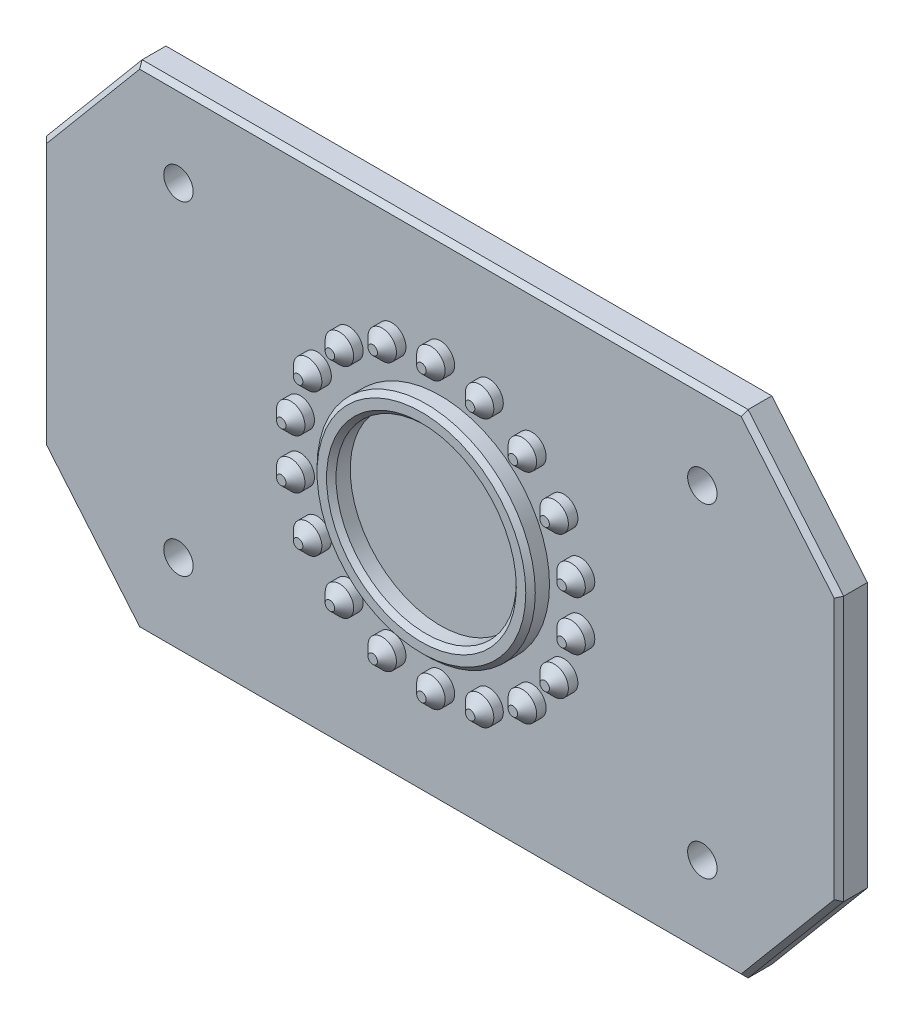
SolidWorks part; units mm, degrees
ref_plane "Front Plane" through (0, 0, 0) normal (0, 0, 1) x (1, 0, 0)
ref_plane "Top Plane" through (0, 0, 0) normal (0, 1, 0) x (1, 0, 0)
ref_plane "Right Plane" through (0, 0, 0) normal (1, 0, 0) x (0, 0, -1)
sketch "Sketch1" plane through (0, 0, 0) normal (0, 0, 1) x (1, 0, 0)
  line L0 (-110, 14.6505) -> (-99.9308, 2.6505) construction
  line L6 (-99.9308, 54.5343) -> (-110, 42.5343) construction
  line L7 (-110, 42.5343) -> (-110, 14.6505) construction
  line L8 (-26, 14.6505) -> (-26, 42.5343) construction
  line L9 (-26, 42.5343) -> (-36.0692, 54.5343) construction
  line L15 (-36.0692, 2.6505) -> (-26, 14.6505) construction
  line L16 (-110, 14.6505) -> (-99.9308, 2.6505)
  line L22 (-99.9308, 54.5343) -> (-110, 42.5343)
  line L23 (-110, 42.5343) -> (-110, 14.6505)
  line L24 (-26, 14.6505) -> (-26, 42.5343)
  line L25 (-26, 42.5343) -> (-36.0692, 54.5343)
  line L31 (-36.0692, 2.6505) -> (-26, 14.6505)
  line L32 (-99.9308, 54.5343) -> (-36.0692, 54.5343)
  line L33 (-99.9308, 2.6505) -> (-36.0692, 2.6505)
  circle A0 centre (-68, 28.5924) radius 9.5 construction
  circle A1 centre (-68, 28.5924) radius 9.5
extrude "Boss-Extrude1" add sketch "Sketch1" along normal blind 3 contours A1 | L16 L33 L31 L24 L25 L32 L22 L23 A1
chamfer "Chamfer1" distance 0.5 angle 45 8 edges at (-110, 28.5924, 3) (-104.9654, 48.5343, 3) (-68, 54.5343, 3) (-31.0346, 48.5343, 3) (-26, 28.5924, 3) (-31.0346, 8.6505, 3) (-68, 2.6505, 3) (-104.9654, 8.6505, 3)
sketch "Sketch2" plane through (0, 0, 0) normal (0, 0, -1) x (-1, 0, 0)
  circle A0 centre (40.3924, 45.6851) radius 1.55 construction
  circle A1 centre (95.6076, 45.6851) radius 1.55 construction
  circle A2 centre (95.6076, 11.4997) radius 1.55 construction
  circle A3 centre (40.3924, 11.4997) radius 1.55 construction
  circle A4 centre (40.3924, 45.6851) radius 1.55
  circle A5 centre (95.6076, 45.6851) radius 1.55
  circle A6 centre (95.6076, 11.4997) radius 1.55
  circle A7 centre (40.3924, 11.4997) radius 1.55
extrude "Cut-Extrude1" cut sketch "Sketch2" against normal up to next
sketch "Sketch3" plane through (0, 0, 3) normal (0, 0, 1) x (1, 0, 0)
  line L0 (-68, 28.5924) -> (-68, 43.5924) construction
  line L8 (-99.9308, 2.6505) -> (-36.0692, 2.6505)
  line L9 (-110, 14.6505) -> (-99.9308, 2.6505)
  line L10 (-110, 42.5343) -> (-110, 14.6505)
  line L11 (-99.9308, 54.5343) -> (-110, 42.5343)
  line L12 (-36.0692, 54.5343) -> (-99.9308, 54.5343)
  line L13 (-26, 42.5343) -> (-36.0692, 54.5343)
  line L14 (-26, 14.6505) -> (-26, 42.5343)
  line L15 (-36.0692, 2.6505) -> (-26, 14.6505)
  line L16 (-99.9308, 2.6505) -> (-36.0692, 2.6505)
  line L17 (-110, 14.6505) -> (-99.9308, 2.6505)
  line L18 (-110, 42.5343) -> (-110, 14.6505)
  line L19 (-99.9308, 54.5343) -> (-110, 42.5343)
  line L20 (-36.0692, 54.5343) -> (-99.9308, 54.5343)
  line L21 (-26, 42.5343) -> (-36.0692, 54.5343)
  line L22 (-26, 14.6505) -> (-26, 42.5343)
  line L23 (-36.0692, 2.6505) -> (-26, 14.6505)
  circle A0 centre (-68, 43.5924) radius 1.5
  circle A1 centre (-68, 28.5924) radius 9.5
  circle A2 centre (-68, 28.5924) radius 9.5
  circle A3 centre (-62.8697, 42.6878) radius 1.5
  circle A4 centre (-58.3582, 40.0831) radius 1.5
  circle A5 centre (-55.0096, 36.0924) radius 1.5
  circle A6 centre (-53.2279, 31.1971) radius 1.5
  circle A7 centre (-53.2279, 25.9877) radius 1.5
  circle A8 centre (-55.0096, 21.0924) radius 1.5
  circle A9 centre (-58.3582, 17.1017) radius 1.5
  circle A10 centre (-62.8697, 14.497) radius 1.5
  circle A11 centre (-68, 13.5924) radius 1.5
  circle A12 centre (-73.1303, 14.497) radius 1.5
  circle A13 centre (-77.6418, 17.1017) radius 1.5
  circle A14 centre (-80.9904, 21.0924) radius 1.5
  circle A15 centre (-82.7721, 25.9877) radius 1.5
  circle A16 centre (-82.7721, 31.1971) radius 1.5
  circle A17 centre (-80.9904, 36.0924) radius 1.5
  circle A18 centre (-77.6418, 40.0831) radius 1.5
  circle A19 centre (-73.1303, 42.6878) radius 1.5
  point P50 (-68, 28.5924)
  dimension "D4" = 3
  dimension "D3" = 15
  dimension "D1" = 0
  dimension "D2" = 0
  dimension "D5" = 18
extrude "Boss-Extrude2" add sketch "Sketch3" along normal blind 2
chamfer "Chamfer2" distance 1 angle 45 18 edges at (-66.5, 43.5924, 5) (-79.4904, 36.0924, 5) (-81.2721, 31.1971, 5) (-81.2721, 25.9877, 5) (-79.4904, 21.0924, 5) (-76.1418, 17.1017, 5) (-71.6303, 14.497, 5) (-66.5, 13.5924, 5) (-61.3697, 14.497, 5) (-56.8582, 17.1017, 5) (-53.5096, 21.0924, 5) (-51.7279, 25.9877, 5) (-51.7279, 31.1971, 5) (-53.5096, 36.0924, 5) (-56.8582, 40.0831, 5) (-61.3697, 42.6878, 5) (-71.6303, 42.6878, 5) (-76.1418, 40.0831, 5)
sketch "Sketch4" plane through (0, 0, 3) normal (0, 0, 1) x (1, 0, 0)
  line L8 (-99.9308, 2.6505) -> (-36.0692, 2.6505)
  line L9 (-36.0692, 2.6505) -> (-26, 14.6505)
  line L10 (-26, 14.6505) -> (-26, 42.5343)
  line L11 (-26, 42.5343) -> (-36.0692, 54.5343)
  line L12 (-36.0692, 54.5343) -> (-99.9308, 54.5343)
  line L13 (-99.9308, 54.5343) -> (-110, 42.5343)
  line L14 (-110, 42.5343) -> (-110, 14.6505)
  line L15 (-110, 14.6505) -> (-99.9308, 2.6505)
  line L16 (-99.9308, 2.6505) -> (-36.0692, 2.6505)
  line L17 (-36.0692, 2.6505) -> (-26, 14.6505)
  line L18 (-26, 14.6505) -> (-26, 42.5343)
  line L19 (-26, 42.5343) -> (-36.0692, 54.5343)
  line L20 (-36.0692, 54.5343) -> (-99.9308, 54.5343)
  line L21 (-99.9308, 54.5343) -> (-110, 42.5343)
  line L22 (-110, 42.5343) -> (-110, 14.6505)
  line L23 (-110, 14.6505) -> (-99.9308, 2.6505)
  circle A0 centre (-68, 28.5924) radius 11.5
  circle A1 centre (-68, 28.5924) radius 9.5
  circle A2 centre (-68, 28.5924) radius 9.5
  circle A3 centre (-68, 43.5924) radius 1.5
  circle A4 centre (-68, 43.5924) radius 1.5
  circle A5 centre (-62.8697, 14.497) radius 1.5
  circle A6 centre (-62.8697, 14.497) radius 1.5
  circle A7 centre (-58.3582, 17.1017) radius 1.5
  circle A8 centre (-58.3582, 17.1017) radius 1.5
  circle A9 centre (-55.0096, 21.0924) radius 1.5
  circle A10 centre (-55.0096, 21.0924) radius 1.5
  circle A11 centre (-53.2279, 25.9877) radius 1.5
  circle A12 centre (-53.2279, 25.9877) radius 1.5
  circle A13 centre (-53.2279, 31.1971) radius 1.5
  circle A14 centre (-53.2279, 31.1971) radius 1.5
  circle A15 centre (-55.0096, 36.0924) radius 1.5
  circle A16 centre (-55.0096, 36.0924) radius 1.5
  circle A17 centre (-58.3582, 40.0831) radius 1.5
  circle A18 centre (-58.3582, 40.0831) radius 1.5
  circle A19 centre (-62.8697, 42.6878) radius 1.5
  circle A20 centre (-62.8697, 42.6878) radius 1.5
  circle A21 centre (-77.6418, 40.0831) radius 1.5
  circle A22 centre (-77.6418, 40.0831) radius 1.5
  circle A23 centre (-80.9904, 36.0924) radius 1.5
  circle A24 centre (-80.9904, 36.0924) radius 1.5
  circle A25 centre (-82.7721, 31.1971) radius 1.5
  circle A26 centre (-82.7721, 31.1971) radius 1.5
  circle A27 centre (-82.7721, 25.9877) radius 1.5
  circle A28 centre (-82.7721, 25.9877) radius 1.5
  circle A29 centre (-80.9904, 21.0924) radius 1.5
  circle A30 centre (-80.9904, 21.0924) radius 1.5
  circle A31 centre (-77.6418, 17.1017) radius 1.5
  circle A32 centre (-77.6418, 17.1017) radius 1.5
  circle A33 centre (-73.1303, 14.497) radius 1.5
  circle A34 centre (-73.1303, 14.497) radius 1.5
  circle A35 centre (-68, 13.5924) radius 1.5
  circle A36 centre (-68, 13.5924) radius 1.5
  circle A37 centre (-73.1303, 42.6878) radius 1.5
  circle A38 centre (-73.1303, 42.6878) radius 1.5
  dimension "D21" = 2
  dimension "D1" = 0
  dimension "D2" = 0
  dimension "D3" = 0
  dimension "D4" = 0
  dimension "D5" = 0
  dimension "D6" = 0
  dimension "D7" = 0
  dimension "D8" = 0
  dimension "D9" = 0
  dimension "D10" = 0
  dimension "D11" = 0
  dimension "D12" = 0
  dimension "D13" = 0
  dimension "D14" = 0
  dimension "D15" = 0
  dimension "D16" = 0
  dimension "D17" = 0
  dimension "D18" = 0
  dimension "D19" = 0
  dimension "D20" = 0
extrude "Boss-Extrude3" add sketch "Sketch4" along normal blind 2 contours A0 A2
chamfer "Chamfer3" distance 0.5 angle 45 2 edges at (-56.5, 28.5924, 5) (-58.5, 28.5924, 5)
